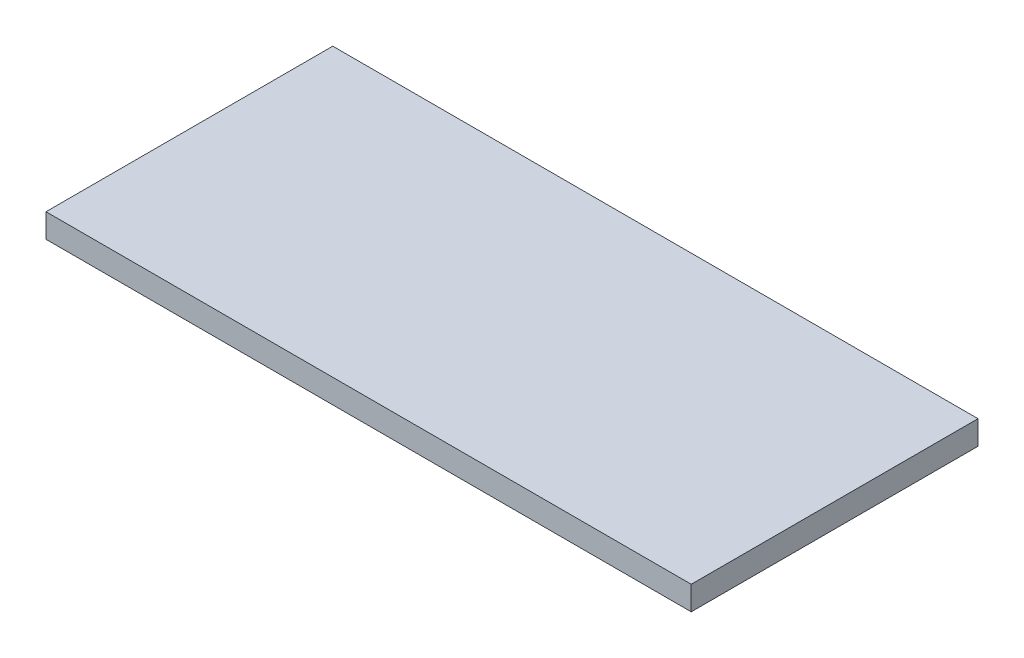
SolidWorks part; units mm, degrees
ref_plane "Front Plane" through (0, 0, 0) normal (0, 0, 1) x (1, 0, 0)
ref_plane "Top Plane" through (0, 0, 0) normal (0, 1, 0) x (1, 0, 0)
ref_plane "Right Plane" through (0, 0, 0) normal (1, 0, 0) x (0, 0, -1)
sketch "Sketch1" plane through (0, 0, 0) normal (0, 1, 0) x (1, 0, 0)
  line L1 (-27, -12) -> (27, -12)
  line L2 (-27, -12) -> (-27, 12)
  line L3 (-27, 12) -> (27, 12)
  line L4 (27, -12) -> (27, 12)
  line L5 (-27, -12) -> (27, 12) construction
  line L6 (-27, 12) -> (27, -12) construction
  point P0 (0, 0)
  dimension "D1" = 54
  dimension "D2" = 24
extrude "Boss-Extrude1" add sketch "Sketch1" along normal blind 2
